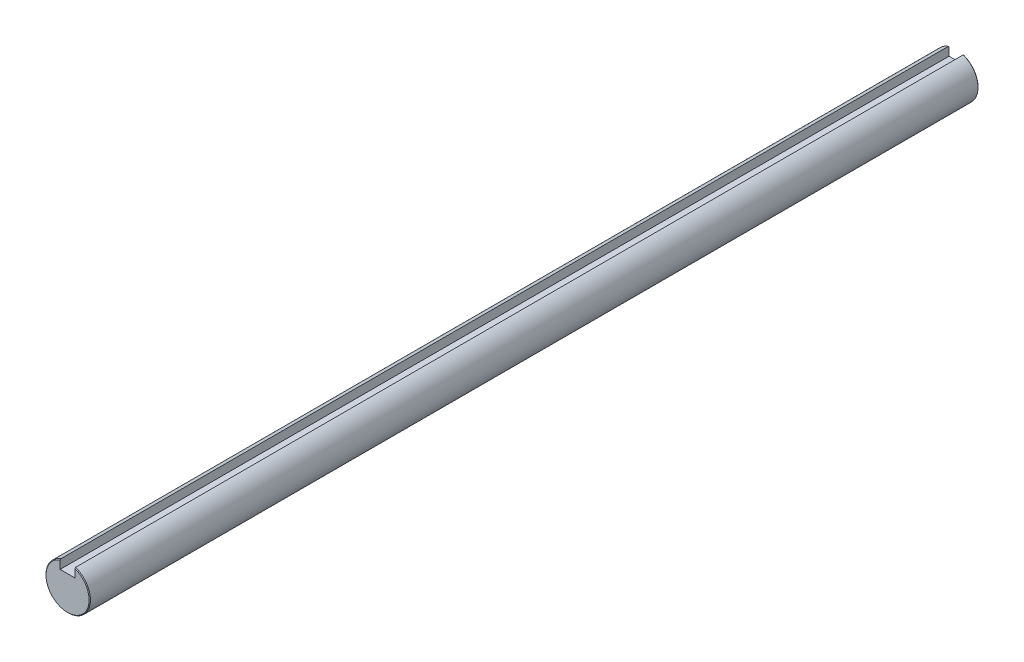
SolidWorks part; units mm, degrees
ref_plane "Front Plane" through (0, 0, 0) normal (0, 0, 1) x (1, 0, 0)
ref_plane "Top Plane" through (0, 0, 0) normal (0, 1, 0) x (1, 0, 0)
ref_plane "Right Plane" through (0, 0, 0) normal (1, 0, 0) x (0, 0, -1)
sketch "Sketch1" plane through (0, 0, 0) normal (1, 0, 0) x (0, 0, -1)
  line L0 (0, 0) -> (0, 7.5) construction
  line L1 (-150, 7.5) -> (150, 7.5)
  line L2 (-150, 7.5) -> (-150, -7.5)
  line L3 (-150, -7.5) -> (150, -7.5)
  line L4 (150, 7.5) -> (150, -7.5)
  line L5 (-150, 7.5) -> (150, -7.5) construction
  line L6 (-150, -7.5) -> (150, 7.5) construction
  line L7 (0, 0) -> (0, -7.5) construction
  point P0 (0, 0)
  point P8 (-132.75, 7.5)
  point P10 (132.75, 7.5)
  point P11 (-150, 0)
  dimension "Diameter" = 15
  dimension "Length" = 300
  dimension "D1" = 17.25
  dimension "D2" = 17.25
  dimension "Keyway Length" = 300
sketch "Sketch2" plane through (0, 0, 0) normal (0, 0, 1) x (1, 0, 0)
  line L0 (0, 0) -> (0, 7.5) construction
  line L2 (2.5, 4.0711) -> (-2.5, 4.0711)
  line L3 (2.5, 4.0711) -> (2.5, 7.0711)
  line L4 (2.5, 7.0711) -> (-2.5, 7.0711)
  line L5 (-2.5, 4.0711) -> (-2.5, 7.0711)
  line L6 (2.5, 4.0711) -> (-2.5, 7.0711) construction
  line L7 (2.5, 7.0711) -> (-2.5, 4.0711) construction
  circle A0 centre (0, 0) radius 7.5
  point P3 (0, 5.5711)
  dimension "Keyway Width" = 5
  dimension "Keyway Depth" = 3
sketch "Sketch3" plane through (0, 0, 0) normal (0, 0, 1) x (1, 0, 0)
  line L1 (-2.5, 4.0711) -> (-2.5, 7.0711) construction
  line L2 (2.5, 4.0711) -> (-2.5, 4.0711) construction
  line L3 (2.5, 4.0711) -> (2.5, 7.0711) construction
  line L5 (-2.5, 4.0711) -> (-2.5, 7.0711)
  line L6 (2.5, 4.0711) -> (-2.5, 4.0711)
  line L7 (2.5, 4.0711) -> (2.5, 7.0711)
  circle A0 centre (0, 0) radius 7.5 construction
  arc A1 (-2.5, 7.0711) -> (2.5, 7.0711) centre (0, 0) ccw
extrude "Boss-Extrude1" add sketch "Sketch3" along normal up to vertex (150 mm away) and the other way up to vertex (150 mm away) up to point (0, 7.5, 150) other way up to point (0, 7.5, -150)
chamfer "Chamfer1" distance 0.225 angle 45 2 edges at (0, -7.5, -150) (0, -7.5, 150)
equation "\"D2@Sketch1\"=1.15*\"Diameter@Sketch1\""
equation "\"D1@Sketch1\"=\"D2@Sketch1\""
equation "\"D1@Chamfer1\"=\"Diameter@Sketch1\"*.015"
